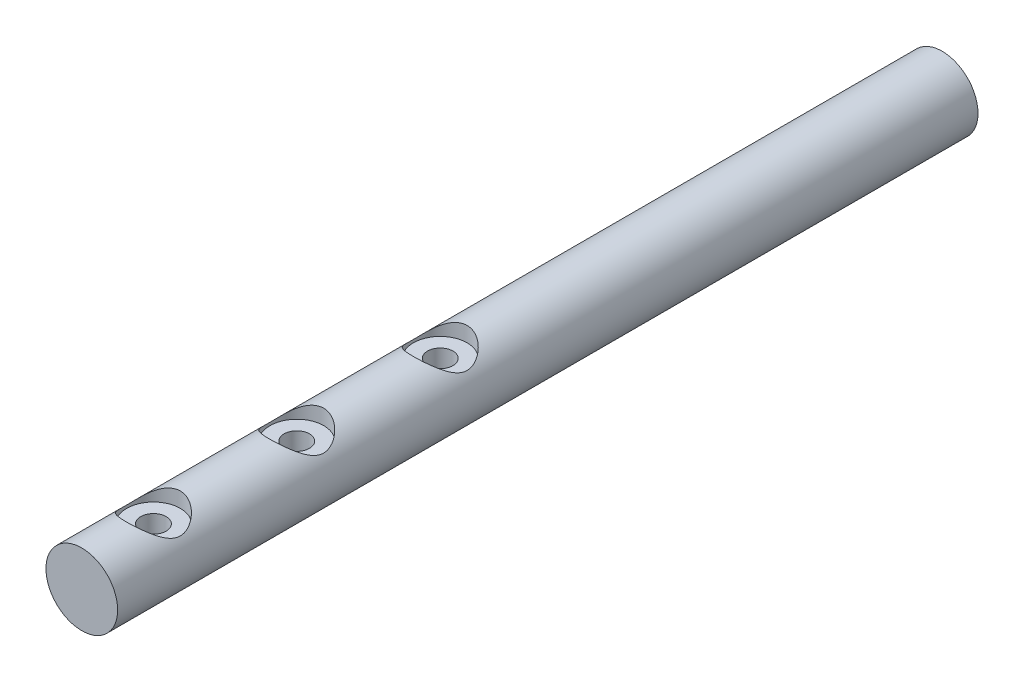
SolidWorks part; units mm, degrees
ref_plane "Front" through (0, 0, 0) normal (0, 0, 1) x (1, 0, 0)
ref_plane "Top" through (0, 0, 0) normal (0, 1, 0) x (1, 0, 0)
ref_plane "Right" through (0, 0, 0) normal (1, 0, 0) x (0, 0, -1)
sketch "Sketch1" plane through (0, 0, 0) normal (0, 0, 1) x (1, 0, 0)
  circle A0 centre (0, 0) radius 6.35
extrude "Boss-Extrude1" add sketch "Sketch1" along normal blind 152.4
hole_wizard "CBORE for #8 Binding Head Machine Screw1" positions "3DSketch1" profile "Sketch5" counterbore size "#8" standard "ANSI Inch" end condition through all
sketch3d "3DSketch1"
  point P0 (-0.0169, 6.35, 139.6971)
  point P2 (-0.027, 6.3499, 114.3025)
  point P4 (-0.0032, 6.35, 88.9018)
sketch "Sketch5" plane through (-0.0169, 6.35, 139.6971) normal (0, 0, 1) x (-1, -0.0027, 0)
  line L0 (0, 0) -> (0, 12.7169)
  line L1 (0, 12.7169) -> (2.2479, 12.7169)
  line L3 (2.2479, 12.7169) -> (2.2479, 2.667)
  line L4 (2.2479, 2.667) -> (4.7625, 2.667)
  line L5 (4.7625, 2.667) -> (4.7625, 0)
  line L7 (4.7625, 0) -> (0, 0)
  line L11 (0, -6.35) -> (0, 107.95) construction
  dimension "Thru Hole Dia." = 4.4958
  dimension "Thru Hole Depth" = 12.7169
  dimension "C'Bore Dia." = 9.525
  dimension "C'Bore Depth" = 2.667
